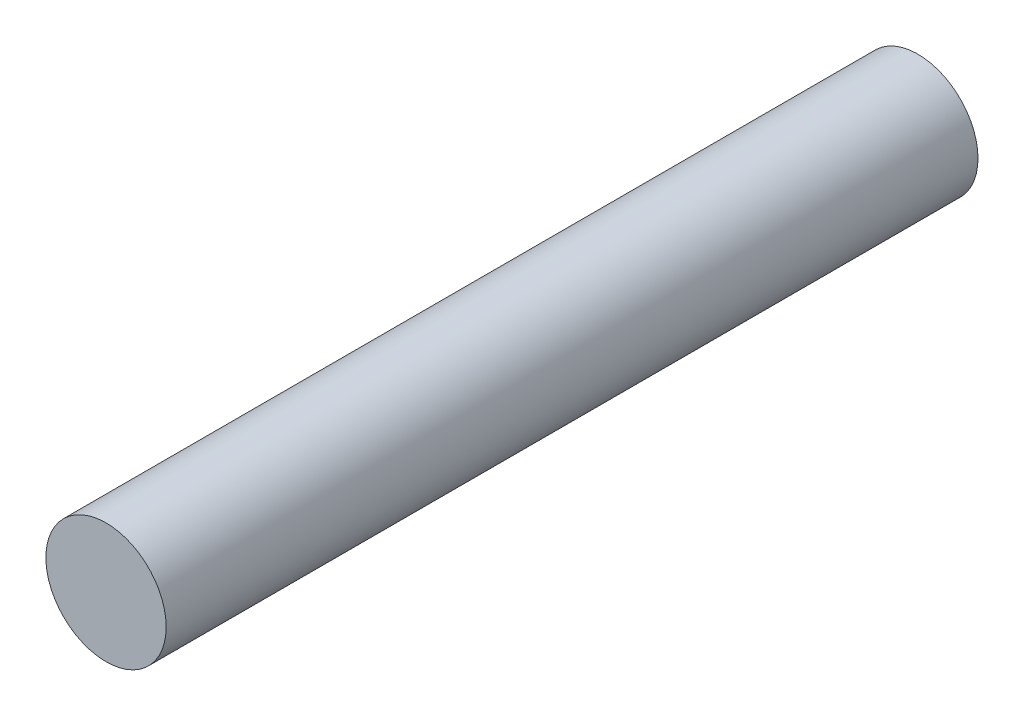
SolidWorks part; units mm, degrees
ref_plane "Front Plane" through (0, 0, 0) normal (0, 0, 1) x (1, 0, 0)
ref_plane "Top Plane" through (0, 0, 0) normal (0, 1, 0) x (1, 0, 0)
ref_plane "Right Plane" through (0, 0, 0) normal (1, 0, 0) x (0, 0, -1)
sketch "Sketch1" plane through (0, 0, 0) normal (0, 0, 1) x (1, 0, 0)
  circle A0 centre (0, 0) radius 3.175
extrude "Boss-Extrude1" add sketch "Sketch1" along normal blind 42.8625
